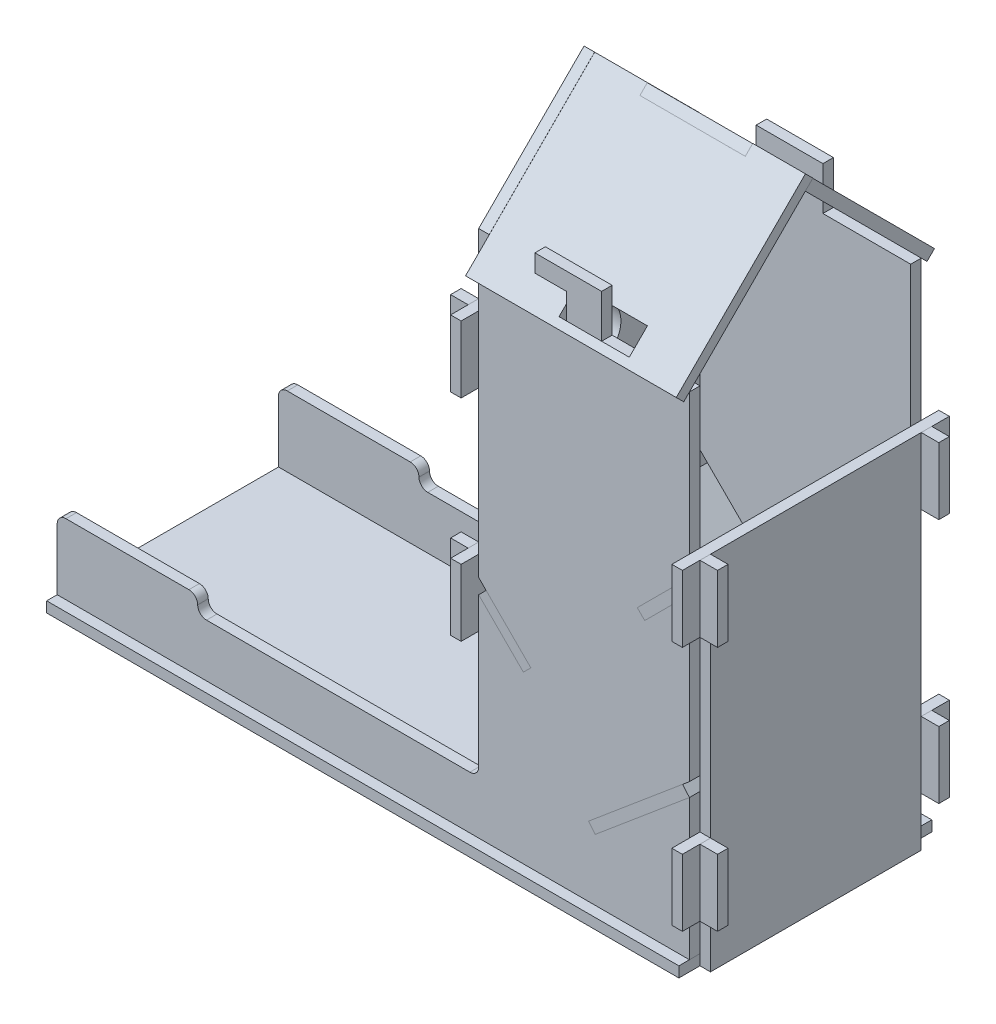
SolidWorks part; units mm, degrees
other "爆炸视图1" [suppressed]
other "爆炸步骤1" [suppressed]
other "爆炸直线1"
other "爆炸步骤2" [suppressed]
other "爆炸直线1"
other "爆炸步骤3" [suppressed]
other "爆炸直线1"
other "爆炸步骤4" [suppressed]
other "爆炸直线1"
other "爆炸步骤5" [suppressed]
other "爆炸直线1"
other "爆炸步骤6" [suppressed]
other "爆炸直线1"
other "爆炸步骤7" [suppressed]
other "爆炸直线1"
other "爆炸步骤8" [suppressed]
other "爆炸直线1"
other "爆炸步骤9" [suppressed]
other "爆炸直线1"
other "爆炸步骤10" [suppressed]
other "爆炸直线1"
other "爆炸步骤11" [suppressed]
other "爆炸直线1"
other "爆炸步骤12" [suppressed]
other "爆炸直线1"
other "爆炸步骤13" [suppressed]
other "爆炸直线1"
other "爆炸步骤14" [suppressed]
other "爆炸直线1"
other "爆炸步骤15" [suppressed]
other "爆炸直线1"
other "爆炸步骤16" [suppressed]
other "爆炸直线1"
other "爆炸步骤17" [suppressed]
other "爆炸直线1"
other "爆炸步骤18" [suppressed]
other "爆炸直线1"
other "爆炸步骤19" [suppressed]
other "爆炸直线1"
other "爆炸步骤20" [suppressed]
other "爆炸直线1"
other "爆炸步骤21" [suppressed]
other "爆炸直线1"
other "爆炸步骤22" [suppressed]
other "爆炸直线1"
other "爆炸步骤23" [suppressed]
other "爆炸直线1"
other "爆炸步骤24" [suppressed]
other "爆炸直线1"
other "爆炸步骤25" [suppressed]
other "爆炸直线1"
other "爆炸步骤26" [suppressed]
other "爆炸直线1"
other "爆炸步骤27" [suppressed]
other "爆炸直线1"
other "爆炸步骤28" [suppressed]
other "爆炸直线1"
other "爆炸步骤29" [suppressed]
other "爆炸直线1"
ref_plane "前视基准面" through (0, 0, 0) normal (0, 0, 1) x (1, 0, 0)
ref_plane "上视基准面" through (0, 0, 0) normal (0, 1, 0) x (1, 0, 0)
ref_plane "右视基准面" through (0, 0, 0) normal (1, 0, 0) x (0, 0, -1)
sketch "草图1" plane through (0, 0, 0) normal (0, 0, 1) x (1, 0, 0)
  line L0 (-160, 0) -> (-160, -5.5)
  line L1 (0, 0) -> (-30, 0)
  line L2 (0, 0) -> (0, 11)
  line L3 (0, 140) -> (-25, 140)
  line L4 (-60, 17.5) -> (-60, 51)
  line L5 (-40, 0) -> (-150, 0)
  line L7 (-142.5, 20) -> (-177.5, 20)
  line L8 (-180, 0) -> (-180, 17.5)
  line L11 (-137.5, 15) -> (-62.5, 15)
  line L13 (-160, -5.5) -> (-141, -5.5)
  line L14 (-141, -5.5) -> (-141, -3)
  line L15 (-141, -3) -> (-150, -3)
  line L16 (-150, -3) -> (-150, 0)
  line L17 (-40, 0) -> (-40, -5.5)
  line L18 (-40, -5.5) -> (-21, -5.5)
  line L19 (-21, -5.5) -> (-21, -3)
  line L20 (-21, -3) -> (-30, -3)
  line L21 (-30, -3) -> (-30, 0)
  line L22 (-160, 0) -> (-180, 0)
  line L23 (0, 90) -> (3, 90)
  line L24 (3, 90) -> (3, 100)
  line L25 (3, 100) -> (8, 100)
  line L26 (8, 100) -> (8, 81)
  line L27 (8, 81) -> (0, 81)
  line L28 (0, 20) -> (3, 20)
  line L29 (3, 20) -> (3, 30)
  line L30 (3, 30) -> (8, 30)
  line L31 (8, 30) -> (8, 11)
  line L32 (8, 11) -> (0, 11)
  line L33 (0, 94.2426) -> (0, 140)
  line L34 (0, 20) -> (0, 40)
  line L35 (-60, 120) -> (-63, 120)
  line L36 (-63, 120) -> (-63, 130)
  line L37 (-63, 130) -> (-68, 130)
  line L38 (-68, 130) -> (-68, 111)
  line L39 (-68, 111) -> (-60, 111)
  line L40 (-60, 60) -> (-63, 60)
  line L41 (-63, 60) -> (-63, 70)
  line L42 (-63, 70) -> (-68, 70)
  line L43 (-68, 70) -> (-68, 51)
  line L44 (-68, 51) -> (-60, 51)
  line L45 (-60, 120) -> (-60, 140)
  line L46 (-60, 64.2426) -> (-60, 111)
  line L47 (0, 90) -> (-12.7279, 77.2721)
  line L48 (-12.7279, 77.2721) -> (-14.8492, 79.3934)
  line L49 (-14.8492, 79.3934) -> (0, 94.2426)
  line L50 (-60, 60) -> (-47.2721, 47.2721)
  line L51 (-47.2721, 47.2721) -> (-45.1508, 49.3934)
  line L52 (-45.1508, 49.3934) -> (-60, 64.2426)
  line L53 (0, 40) -> (-26.8116, 17.5024)
  line L54 (-26.8116, 17.5024) -> (-28.7399, 19.8006)
  line L55 (-28.7399, 19.8006) -> (0, 43.9162)
  line L56 (0, 43.9162) -> (0, 81)
  line L57 (-35, 140) -> (-35, 147.3)
  line L58 (-35, 147.3) -> (-44, 147.3)
  line L59 (-44, 147.3) -> (-44, 152.3)
  line L60 (-44, 152.3) -> (-25, 152.3)
  line L61 (-25, 152.3) -> (-25, 140)
  line L62 (-35, 140) -> (-60, 140)
  arc A0 (-140, 17.5) -> (-142.5, 20) centre (-142.5, 17.5) ccw
  arc A1 (-140, 17.5) -> (-137.5, 15) centre (-137.5, 17.5) ccw
  arc A2 (-177.5, 20) -> (-180, 17.5) centre (-177.5, 17.5) ccw
  arc A3 (-62.5, 15) -> (-60, 17.5) centre (-62.5, 17.5) ccw
  dimension "D7" = 5
  dimension "D8" = 5
  dimension "D9" = 5
  dimension "D5" = 5
  dimension "D1" = 60
  dimension "D2" = 140
  dimension "D3" = 180
  dimension "D4" = 5.5
  dimension "D6" = 3
  dimension "D10" = 19
  dimension "D11" = 10
  dimension "D12" = 5.5
  dimension "D13" = 3
  dimension "D14" = 20
  dimension "D15" = 15
  dimension "D16" = 10
  dimension "D17" = 19
  dimension "D18" = 20
  dimension "D19" = 40
  dimension "D20" = 3
  dimension "D21" = 3
  dimension "D22" = 8
  dimension "D23" = 8
  dimension "D24" = 50
  dimension "D25" = 19
  dimension "D26" = 10
  dimension "D27" = 19
  dimension "D28" = 10
  dimension "D29" = 20
  dimension "D30" = 8
  dimension "D31" = 3
  dimension "D32" = 10
  dimension "D33" = 19
  dimension "D34" = 3
  dimension "D35" = 8
  dimension "D36" = 10
  dimension "D37" = 19
  dimension "D38" = 20
  dimension "D39" = 80
  dimension "D40" = 18
  dimension "D41" = 3
  dimension "D42" = 45
  dimension "D43" = 18
  dimension "D44" = 3
  dimension "D45" = 45
  dimension "D46" = 3
  dimension "D47" = 35
  dimension "D48" = 40
  dimension "D49" = 50
  dimension "D50" = 7.3
  dimension "D51" = 5
  dimension "D52" = 10
  dimension "D53" = 19
  dimension "D54" = 25
extrude "凸台-拉伸1" add sketch "草图1" against normal blind 66
sketch "草图2" plane through (0, 0, 0) normal (1, 0, 0) x (0, 0, -1)
  line L11 (0, 94.2426) -> (0, 140) construction
  line L12 (3, 167.0787) -> (63, 167.0787)
  line L14 (3, 167.0787) -> (3, -38.1526)
  line L15 (3, -38.1526) -> (63, -38.1526)
  line L16 (63, 167.0787) -> (63, -38.1526)
  line L17 (66, 94.2426) -> (66, 140) construction
  dimension "D1" = 3
  dimension "D2" = 3
extrude "切除-拉伸1" cut sketch "草图2" against normal through all both and the other way through all
sketch "草图3" plane through (0, 0, 0) normal (0, -1, 0) x (1, 0, 0)
  line L0 (-180, 0) -> (-160, 0) construction
  line L5 (-180, 3) -> (0, 3)
  line L6 (-180, 3) -> (-180, -69)
  line L7 (-180, -69) -> (0, -69)
  line L8 (0, 3) -> (0, -69)
  line L9 (-150, -3) -> (-170, -3)
  line L10 (-150, -3) -> (-150, 0)
  line L11 (-150, 0) -> (-170, 0)
  line L12 (-170, -3) -> (-170, 0)
  line L14 (-30, 0) -> (-50, 0)
  line L15 (-30, 0) -> (-30, -3)
  line L16 (-30, -3) -> (-50, -3)
  line L17 (-50, 0) -> (-50, -3)
  line L18 (-150, -66) -> (-40, -66) construction
  line L19 (-30, -63) -> (-50, -63)
  line L20 (-30, -63) -> (-30, -66)
  line L21 (-30, -66) -> (-50, -66)
  line L22 (-50, -63) -> (-50, -66)
  line L23 (-180, -66) -> (-160, -66) construction
  line L24 (-150, -63) -> (-170, -63)
  line L25 (-150, -63) -> (-150, -66)
  line L26 (-150, -66) -> (-170, -66)
  line L27 (-170, -63) -> (-170, -66)
  dimension "D1" = 3
  dimension "D2" = 3
  dimension "D3" = 20
extrude "凸台-拉伸5" add sketch "草图3" along normal blind 3 separate body
sketch "草图6" plane through (0, 0, 0) normal (1, 0, 0) x (0, 0, -1)
  line L0 (3, 100) -> (-5, 100)
  line L1 (3, 100) -> (63, 100)
  line L2 (3, 90) -> (3, 30)
  line L3 (3, -3) -> (63, -3)
  line L4 (63, 90) -> (63, 30)
  line L5 (0, 81) -> (-5, 81)
  line L6 (-5, 81) -> (-5, 100)
  line L7 (0, 81) -> (0, 90)
  line L8 (0, 90) -> (3, 90)
  line L9 (3, 20) -> (0, 20)
  line L10 (0, 20) -> (0, 11)
  line L11 (0, 11) -> (-5, 11)
  line L12 (3, 30) -> (-5, 30)
  line L13 (-5, 30) -> (-5, 11)
  line L14 (63, 20) -> (66, 20)
  line L15 (66, 20) -> (66, 11)
  line L16 (66, 11) -> (71, 11)
  line L17 (71, 11) -> (71, 30)
  line L18 (71, 30) -> (63, 30)
  line L19 (3, 20) -> (3, -3)
  line L20 (63, 20) -> (63, -3)
  line L21 (66, 100) -> (71, 100)
  line L22 (71, 100) -> (71, 81)
  line L23 (71, 81) -> (66, 81)
  line L24 (66, 81) -> (66, 90)
  line L25 (66, 90) -> (63, 90)
  line L26 (63, 100) -> (66, 100)
  dimension "D1" = 5
  dimension "D2" = 5
  dimension "D3" = 5
  dimension "D4" = 5
extrude "凸台-拉伸7" add sketch "草图6" along normal blind 3 separate body
sketch "草图7" plane through (-45, 45, 0) normal (-0.7071, 0.7071, 0) x (0, 0, 1)
  line L0 (-3, 45.6396) -> (0, 45.6396)
  line L1 (-63, 63.6396) -> (-3, 63.6396)
  line L2 (-63, 45.6396) -> (-63, 37.6396)
  line L3 (-63, 37.6396) -> (-3, 37.6396)
  line L4 (-3, 45.6396) -> (-3, 37.6396)
  line L5 (0, 45.6396) -> (0, 63.6396)
  line L6 (0, 63.6396) -> (-3, 63.6396)
  line L7 (-63, 45.6396) -> (-66, 45.6396)
  line L8 (-66, 45.6396) -> (-66, 63.6396)
  line L9 (-66, 63.6396) -> (-63, 63.6396)
  dimension "D1" = 26
extrude "凸台-拉伸8" add sketch "草图7" along normal blind 3 separate body
sketch "草图8" plane through (0, 0, 0) normal (0.7071, 0.7071, 0) x (0, 0, -1)
  line L0 (63, 84.8528) -> (66, 84.8528)
  line L1 (63, 84.8528) -> (3, 84.8528)
  line L2 (63, 66.8528) -> (63, 58.8528)
  line L3 (63, 58.8528) -> (3, 58.8528)
  line L4 (3, 66.8528) -> (3, 58.8528)
  line L5 (66, 84.8528) -> (66, 66.8528)
  line L6 (66, 66.8528) -> (63, 66.8528)
  line L7 (3, 84.8528) -> (0, 84.8528)
  line L8 (0, 84.8528) -> (0, 66.8528)
  line L9 (0, 66.8528) -> (3, 66.8528)
  line L10 (3, 66.8528) -> (0, 66.8528) construction
  dimension "D1" = 26
extrude "凸台-拉伸10" add sketch "草图8" along normal blind 3 separate body
sketch "草图9" plane through (-19.6962, 23.473, 0) normal (-0.6428, 0.766, 0) x (0.766, 0.6428, 0)
  line L0 (25.7115, 3) -> (25.7115, 0)
  line L1 (-9.2885, 63) -> (-32.2885, 63)
  line L2 (25.7115, 63) -> (25.7115, 3)
  line L3 (-9.2885, 3) -> (-32.2885, 3)
  line L4 (-32.2885, 63) -> (-32.2885, 3)
  line L5 (25.7115, 0) -> (-9.2885, 0)
  line L6 (-9.2885, 0) -> (-9.2885, 3)
  line L7 (-9.2885, 63) -> (-9.2885, 66)
  line L8 (-9.2885, 66) -> (25.7115, 66)
  line L9 (25.7115, 66) -> (-9.2885, 66) construction
  line L10 (25.7115, 66) -> (25.7115, 63)
  point P5 (25.7115, 33)
  dimension "D1" = 58
extrude "凸台-拉伸11" add sketch "草图9" along normal blind 3 separate body
sketch "草图10" plane through (-60, 0, 0) normal (-1, 0, 0) x (0, 0, 1)
  line L0 (-3, 120) -> (0, 120)
  line L1 (-63, 40) -> (-3, 40)
  line L2 (-63, 40) -> (-63, 60)
  line L4 (-3, 40) -> (-3, 60)
  line L5 (0, 120) -> (0, 111)
  line L6 (-3, 60) -> (0, 60)
  line L7 (0, 60) -> (0, 51)
  line L8 (-63, 60) -> (-66, 60)
  line L9 (-66, 60) -> (-66, 51)
  line L10 (-63, 120) -> (-66, 120)
  line L11 (-66, 120) -> (-66, 111)
  line L12 (-66, 111) -> (-71, 111)
  line L13 (-63, 130) -> (-71, 130)
  line L14 (-71, 130) -> (-71, 111)
  line L15 (-3, 130) -> (5, 130)
  line L16 (5, 130) -> (5, 111)
  line L17 (5, 111) -> (0, 111)
  line L18 (-3, 70) -> (5, 70)
  line L19 (5, 70) -> (5, 51)
  line L20 (5, 51) -> (0, 51)
  line L21 (-63, 70) -> (-71, 70)
  line L22 (-71, 70) -> (-71, 51)
  line L23 (-71, 51) -> (-66, 51)
  line L24 (-63, 130) -> (-63, 147.3)
  line L25 (-3, 130) -> (-3, 147.3)
  line L26 (-3, 70) -> (-3, 120)
  line L27 (-63, 70) -> (-63, 120)
  line L28 (-63, 147.3) -> (-33, 177.3)
  line L29 (-3, 147.3) -> (-33, 177.3)
  line L30 (-66, 140) -> (-63, 140) construction
  line L31 (-3, 140) -> (0, 140) construction
  circle A0 centre (-33, 137.3) radius 7.5
  circle A1 centre (-33, 107.3) radius 7.5
  dimension "D5" = 15
  dimension "D6" = 15
  dimension "D1" = 8
  dimension "D2" = 8
  dimension "D3" = 8
  dimension "D4" = 8
  dimension "D7" = 100
  dimension "D8" = 30
  dimension "D9" = 40
  dimension "D10" = 135
  dimension "D11" = 37.3
extrude "凸台-拉伸12" add sketch "草图10" along normal blind 3 separate body
ref_plane "基准面2" through (0, 70, 70) normal (0, 0.7071, 0.7071) x (-1, 0, 0)
sketch "草图11" plane through (0, 70, 70) normal (0, 0.7071, 0.7071) x (-1, 0, 0)
  line L1 (60, -148.7046) -> (45, -148.7046)
  line L2 (60, -148.7046) -> (60, -96.7046)
  line L3 (60, -96.7046) -> (0, -96.7046)
  line L4 (0, -148.7046) -> (0, -96.7046)
  line L5 (35, -98.9949) -> (15, -98.9949)
  line L6 (35, -98.9949) -> (35, -106.2949)
  line L7 (35, -106.2949) -> (15, -106.2949)
  line L8 (15, -98.9949) -> (15, -106.2949)
  line L9 (15, -148.7046) -> (0, -148.7046)
  line L11 (45, -148.7046) -> (45, -145.7046)
  line L12 (45, -145.7046) -> (15, -145.7046)
  line L13 (15, -148.7046) -> (15, -145.7046)
  dimension "D1" = 20
  dimension "D2" = 7.3
  dimension "D3" = 52
  dimension "D4" = 3
  dimension "D5" = 15
  dimension "D6" = 15
extrude "凸台-拉伸13" add sketch "草图11" along normal blind 3 separate body
ref_plane "基准面3" through (0, 103, -103) normal (0, 0.7071, -0.7071) x (-1, 0, 0)
sketch "草图12" plane through (0, 103, -103) normal (0, 0.7071, -0.7071) x (-1, 0, 0)
  line L0 (15, 101.9949) -> (45, 101.9949) construction
  line L1 (15, 101.9949) -> (45, 101.9949)
  line L2 (0, 98.9949) -> (0, 49.9949)
  line L3 (0, 49.9949) -> (60, 49.9949)
  line L4 (60, 98.9949) -> (60, 49.9949)
  line L7 (0, 98.9949) -> (15, 98.9949)
  line L8 (15, 101.9949) -> (15, 98.9949)
  line L11 (60, 98.9949) -> (45, 98.9949)
  line L12 (45, 101.9949) -> (45, 98.9949)
  line L13 (35, 52.3259) -> (15, 52.3259)
  line L14 (35, 52.3259) -> (35, 59.6259)
  line L15 (35, 59.6259) -> (15, 59.6259)
  line L16 (15, 52.3259) -> (15, 59.6259)
  dimension "D1" = 15
  dimension "D2" = 15
  dimension "D3" = 3
  dimension "D4" = 3
  dimension "D5" = 20
  dimension "D6" = 7.3
  dimension "D7" = 52
extrude "凸台-拉伸14" add sketch "草图12" along normal blind 3 separate body
other "保存实体1"
move or copy body "实体-移动/复制1" [suppressed] bodies to move or copy 125 copy no translate (0, 21.7918, 0)
move or copy body "实体-移动/复制2" [suppressed] bodies to move or copy 124 copy no translate (0, 17.5681, 0)
move or copy body "实体-移动/复制3" [suppressed] bodies to move or copy 127 copy no translate (0, 0, 68.0533)
move or copy body "实体-移动/复制4" [suppressed] bodies to move or copy 126 copy no translate (0, 0, -20.3444)
move or copy body "实体-移动/复制5" [suppressed] bodies to move or copy 123 copy no translate (-27.1516, 0, 0)
move or copy body "实体-移动/复制6" [suppressed] bodies to move or copy 130 copy no translate (0, 24.9142, 0)
move or copy body "实体-移动/复制9" [suppressed] bodies to move or copy 118 copy no translate (28.7943, 0, 0)
move or copy body "实体-移动/复制10" [suppressed] bodies to move or copy 134 copy no translate (0, 30.7866, 0)
move or copy body "实体-移动/复制11" [suppressed] bodies to move or copy 135 copy no translate (28.7329, 0, 0)
move or copy body "实体-移动/复制12" [suppressed] bodies to move or copy 136 copy no translate (0, 19.3568, 0)
move or copy body "实体-移动/复制13" [suppressed] bodies to move or copy 137 copy no translate (35.315, 0, 0)
move or copy body "实体-移动/复制14" [suppressed] bodies to move or copy 119 copy no translate (40.8742, 0, 0)
move or copy body "实体-移动/复制15" [suppressed] bodies to move or copy 139 copy no translate (0, 40.5212, 0)
move or copy body "实体-移动/复制16" [suppressed] bodies to move or copy 122 copy no translate (51.6955, 0, 0)
move or copy body "实体-移动/复制17" [suppressed] bodies to move or copy 141 copy no translate (0, 46.7318, 0)
move or copy body "实体-移动/复制18" [suppressed] bodies to move or copy 142 copy no translate (11.4641, 0, 0)
move or copy body "实体-移动/复制19" [suppressed] bodies to move or copy 114 copy no translate (0, -31.7704, 0)
move or copy body "实体-移动/复制20" [suppressed] bodies to move or copy 117 copy no translate (0, 0, 56.2502)
move or copy body "实体-移动/复制21" [suppressed] bodies to move or copy 121 copy no translate (-100.9739, 0, 0)
move or copy body "实体-移动/复制22" [suppressed] bodies to move or copy 116 copy no translate (0, 0, 2.2379)
move or copy body "实体-移动/复制23" [suppressed] bodies to move or copy 131 copy no translate (0, 0, 76.5192)
move or copy body "实体-移动/复制24" [suppressed] bodies to move or copy 146 copy no translate (0, -27.0047, 0)
move or copy body "实体-移动/复制25" [suppressed] bodies to move or copy 144 copy no translate (0, 0, 61.21)
move or copy body "实体-移动/复制26" [suppressed] bodies to move or copy 150 copy no translate (55.9304, 0, 0)
move or copy body "实体-移动/复制27" [suppressed] bodies to move or copy 148 copy no translate (-23.818, 0, 0)
move or copy body "实体-移动/复制28" [suppressed] bodies to move or copy 149 copy no translate (0, 0, 29.0859)
move or copy body "实体-移动/复制29" [suppressed] bodies to move or copy 152 copy no translate (0, 0, 51.4219)
move or copy body "实体-移动/复制30" [suppressed] bodies to move or copy 154 copy no translate (0, 41.0686, 0)
move or copy body "实体-移动/复制31" [suppressed] bodies to move or copy 128 copy no translate (0, 39.2527, 0)
